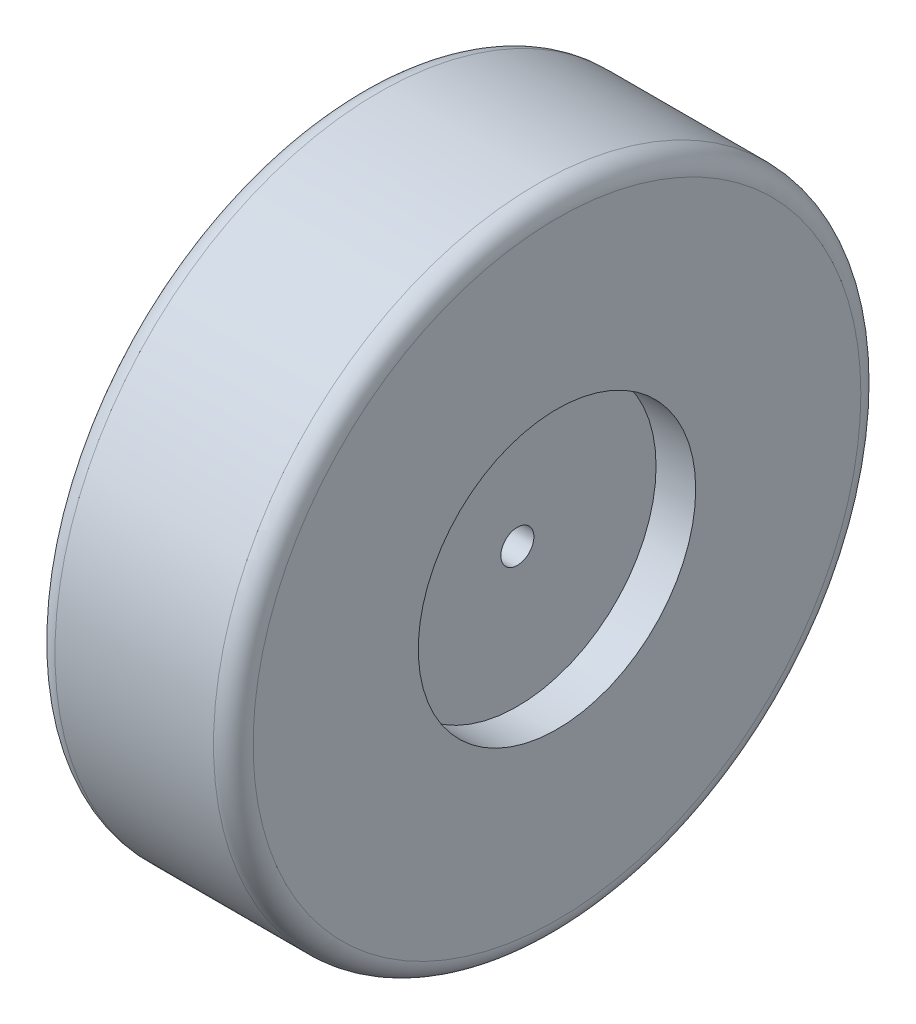
SolidWorks part; units mm, degrees
ref_plane "前视基准面" through (0, 0, 0) normal (0, 0, 1) x (1, 0, 0)
ref_plane "上视基准面" through (0, 0, 0) normal (0, 1, 0) x (1, 0, 0)
ref_plane "右视基准面" through (0, 0, 0) normal (1, 0, 0) x (0, 0, -1)
sketch "草图1" plane through (0, 0, 0) normal (1, 0, 0) x (0, 0, -1)
  circle A0 centre (0, 0) radius 49
  dimension "D1" = 98
extrude "凸台-拉伸1" add sketch "草图1" along normal blind 30
fillet "圆角1" radius 3 2 edges at (0, 0, -49) (30, 0, -49)
sketch "草图2" plane through (30, 0, 0) normal (1, 0, 0) x (0, 0, -1)
  circle A0 centre (0, 0) radius 21
  dimension "D1" = 42
extrude "切除-拉伸1" cut sketch "草图2" against normal blind 6
sketch "草图3" plane through (24, 0, 0) normal (1, 0, 0) x (0, 0, -1)
  circle A0 centre (0, 0) radius 2.5
  dimension "D1" = 5
extrude "切除-拉伸2" cut sketch "草图3" against normal blind 6
